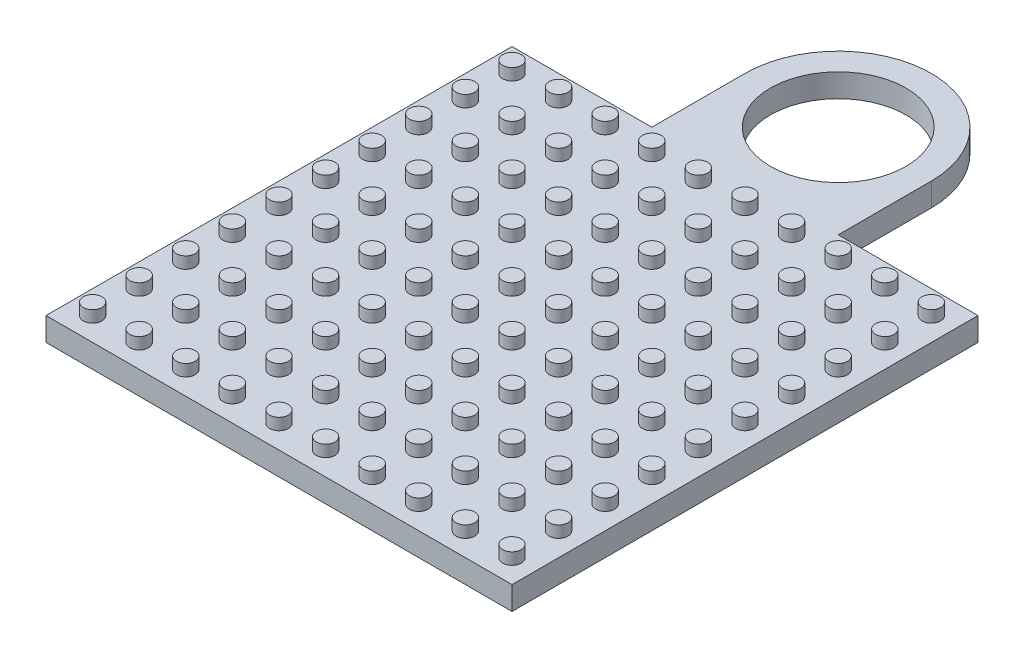
SolidWorks part; units mm, degrees
ref_plane "Front Plane" through (0, 0, 0) normal (0, 0, 1) x (1, 0, 0)
ref_plane "Top Plane" through (0, 0, 0) normal (0, 1, 0) x (1, 0, 0)
ref_plane "Right Plane" through (0, 0, 0) normal (1, 0, 0) x (0, 0, -1)
sketch "Sketch1" plane through (0, 0, 0) normal (0, 1, 0) x (1, 0, 0)
  line L1 (5, -5) -> (-5, -5)
  line L2 (5, -5) -> (5, 5)
  line L3 (5, 5) -> (-5, 5)
  line L4 (-5, -5) -> (-5, 5)
  line L5 (5, -5) -> (-5, 5) construction
  line L6 (5, 5) -> (-5, -5) construction
  point P0 (0, 0)
  dimension "D1" = 10
  dimension "D2" = 10
extrude "Plate" add sketch "Sketch1" along normal blind 0.5
sketch "Sketch2" plane through (0, 0.5, 0) normal (0, 1, 0) x (1, 0, 0)
  line L0 (-5, -5) -> (5, -5) construction
  line L1 (-5, 5) -> (-5, -5) construction
  circle A0 centre (-4.5, -4.5) radius 0.2
  dimension "D1" = 0.4
  dimension "D2" = 0.5
  dimension "D3" = 0.5
extrude "Rod" add sketch "Sketch2" along normal blind 0.25 contours A0
pattern_linear "LPattern1" count 10 spacing 1 along (1, 0, 0) count 10 spacing 1 along (0, 0, -1) of "Rod"
sketch "Sketch4" plane through (0, 0, 0) normal (0, 1, 0) x (1, 0, 0)
  line L5 (-2, 7) -> (-2, 5)
  line L6 (5, 5) -> (-5, 5) construction
  line L8 (-5, 5) -> (-5, -5) construction
  line L9 (-2, 5) -> (2, 5)
  line L10 (2, 5) -> (2, 7)
  arc A0 (-2, 7) -> (2, 7) centre (0, 7) cw
  point P0 (0, 7)
  dimension "D3" = 5
extrude "Boss-Extrude3" add sketch "Sketch4" along normal blind 0.5
sketch "Sketch5" plane through (0, 0.5, 0) normal (0, 1, 0) x (1, 0, 0)
  circle A0 centre (0, 7) radius 1.4559
extrude "Cut-Extrude1" cut sketch "Sketch5" against normal blind 1.5 and the other way blind 0.5
